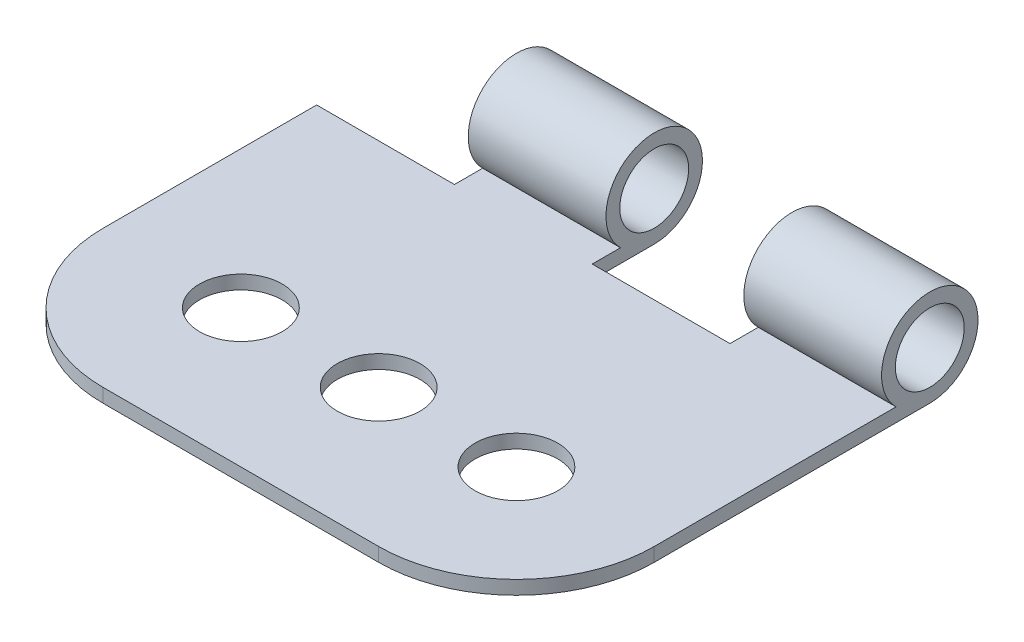
SolidWorks part; units mm, degrees
ref_plane "Plan de face" through (0, 0, 0) normal (0, 0, 1) x (1, 0, 0)
ref_plane "Plan de dessus" through (0, 0, 0) normal (0, 1, 0) x (1, 0, 0)
ref_plane "Plan de droite" through (0, 0, 0) normal (1, 0, 0) x (0, 0, -1)
sketch "Esquisse1" plane through (0, 0, 0) normal (1, 0, 0) x (0, 0, -1)
  line L0 (-17.6196, -3.8423) -> (-17.6196, 3.1577) construction
  line L1 (-57.6196, -2.8423) -> (-20.0691, -2.8423)
  line L2 (-57.6196, -2.8423) -> (-57.6196, -3.8423)
  line L3 (-57.6196, -3.8423) -> (-17.6196, -3.8423)
  arc A0 (-17.6196, -3.8423) -> (-20.0691, -2.8423) centre (-17.6196, -0.3423) ccw
  circle A1 centre (-17.6196, -0.3423) radius 2.5
  dimension "D1" = 1
  dimension "D2" = 7
  dimension "D3" = 40
extrude "Boss.-Extru.1" add sketch "Esquisse1" along normal blind 40
sketch "Esquisse2" plane through (0, 0, 57.6196) normal (0, 0, 1) x (1, 0, 0)
  line L0 (20, -2.8423) -> (20, 4.1577)
  line L1 (0, -2.8423) -> (10, -2.8423)
  line L2 (0, -2.8423) -> (0, 4.1577)
  line L3 (0, 4.1577) -> (10, 4.1577)
  line L4 (10, -2.8423) -> (10, 4.1577)
  line L5 (20, 4.1577) -> (30, 4.1577)
  line L6 (30, -2.8423) -> (30, 4.1577)
  line L7 (20, -2.8423) -> (30, -2.8423)
  dimension "D1" = 7
  dimension "D2" = 10
  dimension "D3" = 2
extrude "Enlèv. mat.-Extru.1" cut sketch "Esquisse2" against normal through all
sketch "Esquisse3" plane through (0, -2.8423, 0) normal (0, 1, 0) x (1, 0, 0)
  line L0 (10, -15.1701) -> (10, -17.6196) construction
  line L1 (10, -22.1196) -> (0, -22.1196)
  line L2 (10, -22.1196) -> (10, -14.1196)
  line L3 (10, -14.1196) -> (0, -14.1196)
  line L4 (0, -22.1196) -> (0, -14.1196)
  line L5 (40, -57.6196) -> (0, -57.6196) construction
  line L6 (30, -22.1196) -> (30, -14.1196)
  line L7 (30, -14.1196) -> (20, -14.1196)
  line L8 (20, -22.1196) -> (20, -14.1196)
  line L9 (30, -22.1196) -> (20, -22.1196)
  dimension "D1" = 0
  dimension "D2" = 10
  dimension "D3" = 35.5
  dimension "D4" = 8
  dimension "D5" = 2
extrude "Enlèv. mat.-Extru.2" cut sketch "Esquisse3" against normal blind 40
sketch "Esquisse4" plane through (0, -2.8423, 0) normal (0, 1, 0) x (1, 0, 0)
  line L0 (0, -57.6196) -> (0, -17.6196) construction
  line L1 (40, -57.6196) -> (40, -17.6196) construction
  line L2 (40, -21.1196) -> (40, -14.1196) construction
  line L3 (40, -17.6196) -> (0, -17.6196) construction
  line L4 (0, -57.6196) -> (40, -57.6196) construction
  line L5 (0, -37.6196) -> (40, -37.6196) construction
  line L6 (10, -47.6196) -> (30, -47.6196)
  line L7 (0, -37.6196) -> (0, -57.6196)
  line L8 (0, -57.6196) -> (40, -57.6196)
  line L9 (40, -57.6196) -> (40, -37.6196)
  circle A0 centre (10, -37.6196) radius 3
  circle A1 centre (20, -37.6196) radius 3
  circle A2 centre (30, -37.6196) radius 3
  arc A4 (30, -47.6196) -> (40, -37.6196) centre (30, -37.6196) ccw
  arc A5 (0, -37.6196) -> (10, -47.6196) centre (10, -37.6196) ccw
  dimension "D2" = 10
  dimension "D1" = 40
  dimension "D3" = 20
  dimension "D4" = 10
extrude "Enlèv. mat.-Extru.3" cut sketch "Esquisse4" against normal through all
